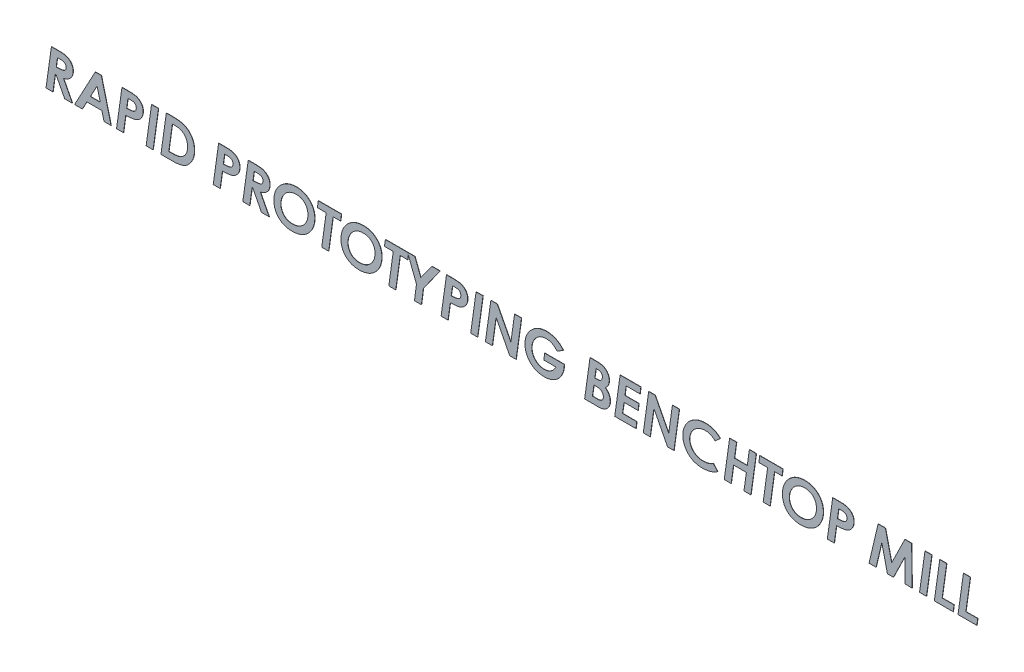
SolidWorks part; units mm, degrees
ref_plane "Front Plane" through (0, 0, 0) normal (0, 0, 1) x (1, 0, 0)
ref_plane "Top Plane" through (0, 0, 0) normal (0, 1, 0) x (1, 0, 0)
ref_plane "Right Plane" through (0, 0, 0) normal (1, 0, 0) x (0, 0, -1)
sketch "Sketch1" plane through (0, 0, 0) normal (0, 0, 1) x (1, 0, 0)
  text T0 "RAPID PROTOTYPING BENCHTOP MILL" font "Century Gothic" height 30
extrude "Boss-Extrude1" add sketch "Sketch1" along normal blind 0.2
